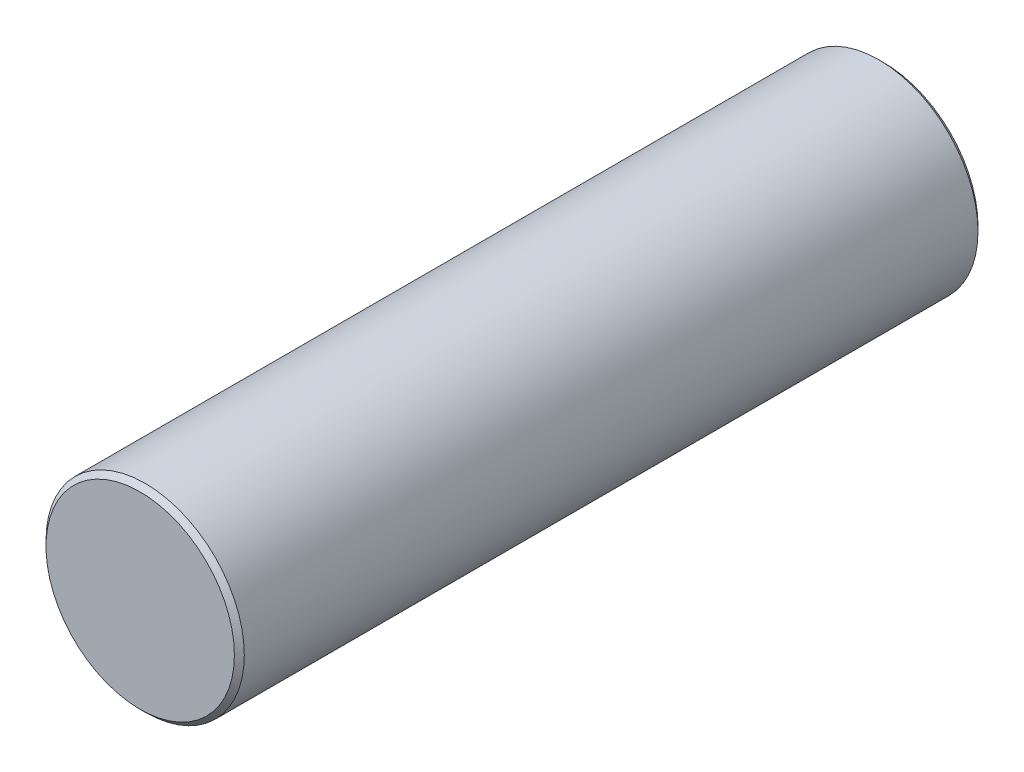
SolidWorks part; units mm, degrees
material "Cast Alloy Steel"
ref_plane "Front Plane" through (0, 0, 0) normal (0, 0, 1) x (1, 0, 0)
ref_plane "Top Plane" through (0, 0, 0) normal (0, 1, 0) x (1, 0, 0)
ref_plane "Right Plane" through (0, 0, 0) normal (1, 0, 0) x (0, 0, -1)
sketch "Sketch1" plane through (0, 0, 0) normal (0, 0, 1) x (1, 0, 0)
  circle A0 centre (0, 0) radius 20
  dimension "D1" = 40
extrude "Boss-Extrude1" add sketch "Sketch1" along normal blind 150
chamfer "Chamfer1" distance 1 angle 45 2 edges at (20, 0, 0) (20, 0, 150)
